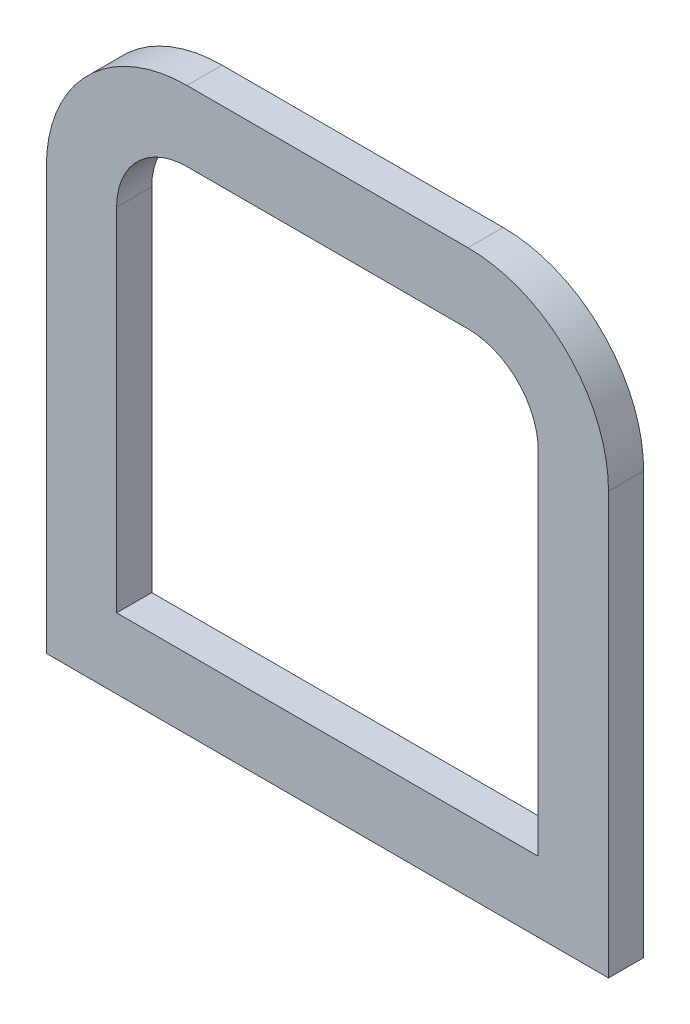
SolidWorks part; units mm, degrees
ref_plane "Front Plane" through (0, 0, 0) normal (0, 0, 1) x (1, 0, 0)
ref_plane "Top Plane" through (0, 0, 0) normal (0, 1, 0) x (1, 0, 0)
ref_plane "Right Plane" through (0, 0, 0) normal (1, 0, 0) x (0, 0, -1)
sketch "Sketch1" plane through (0, 0, 0) normal (0, 0, 1) x (1, 0, 0)
  line L5 (-4, 8) -> (4, 8)
  line L6 (-4, 6) -> (4, 6)
  line L10 (-6, 4) -> (-6, -6)
  line L11 (-6, -6) -> (6, -6)
  line L12 (6, 4) -> (6, -6)
  line L13 (-6, 6) -> (6, -6) construction
  line L14 (-6, -6) -> (6, 6) construction
  line L15 (8, 4) -> (8, -8)
  line L16 (-8, -8) -> (8, -8)
  line L17 (-8, 4) -> (-8, -8)
  arc A0 (4, 6) -> (6, 4) centre (4, 4) cw
  arc A1 (-4, 6) -> (-6, 4) centre (-4, 4) ccw
  arc A2 (4, 8) -> (8, 4) centre (4, 4) cw
  arc A3 (-4, 8) -> (-8, 4) centre (-4, 4) ccw
  point P0 (0, 0)
  dimension "D3" = 2
  dimension "D1" = 12
  dimension "D2" = 12
extrude "Boss-Extrude2" add sketch "Sketch1" along normal blind 1
